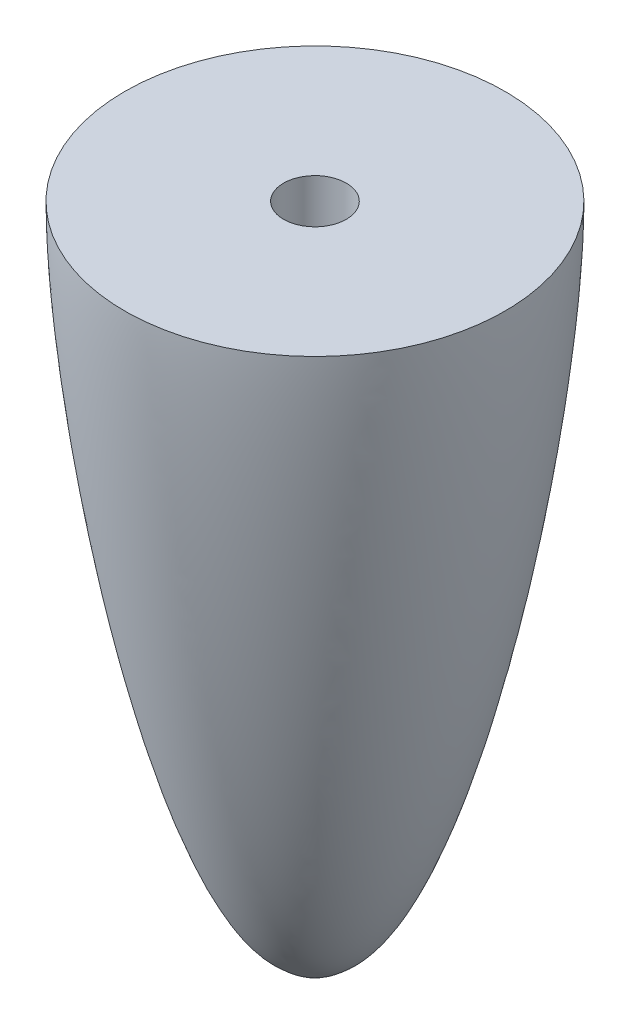
SolidWorks part; units mm, degrees
ref_plane "Plan de face" through (0, 0, 0) normal (0, 0, 1) x (1, 0, 0)
ref_plane "Plan de dessus" through (0, 0, 0) normal (0, 1, 0) x (1, 0, 0)
ref_plane "Plan de droite" through (0, 0, 0) normal (1, 0, 0) x (0, 0, -1)
sketch "Esquisse5" plane through (0, 0, 0) normal (0, 0, 1) x (1, 0, 0)
  line L0 (0, 14) -> (0, -21)
  line L1 (0, 14) -> (-10, 14)
  line L2 (0.8829, -21) -> (-0.8829, -21) construction
  spline S0 degree 3 poles (-10, 14) (-10, 5.6487) (-6.4885, -16.0631) (-1.7517, -20.0984) (-1.5, -20.3) knots 0 0 0 0 0.95 1 1 1 1
  spline S1 degree 3 poles (-1.5, -20.3) (-1.4602, -20.3319) (-0.6629, -20.9645) (-0.2077, -21) (0, -21) knots 0 0 0 0 0.05 1 1 1 1
  point P3 (-1.5, -20.3)
  dimension "D1" = 35
  dimension "D2" = 14
  dimension "D3" = 10
  dimension "D4" = 1.5
  dimension "D5" = 0.7
revolve "Révolution1" add sketch "Esquisse5" angle 360 about L0
hole_wizard "Trou taraudé M41" positions "Esquisse6" profile "Esquisse7" tap size "M4" standard "ISO"
sketch "Esquisse6" plane through (0, 14, 0) normal (0, 1, 0) x (1, 0, 0)
  point P0 (0, 0)
sketch "Esquisse7" plane through (0, 14, 0) normal (1, 0, 0) x (0, 0, 1)
  line L0 (0, 0) -> (0, 22.9914)
  line L1 (0, 22.9914) -> (1.65, 22)
  line L2 (1.65, 22) -> (1.65, 0)
  line L5 (1.65, 0) -> (0, 0)
  line L10 (0, 22.9914) -> (-1.65, 22) construction
  line L11 (0, -6.35) -> (0, 107.95) construction
  dimension "Diamètre du trou pour taraudage" = 3.3
  dimension "Profondeur du trou pour taraudage" = 22
  dimension "Angle de pointe" = 118
cosmetic thread "Filetage de perçage1"
